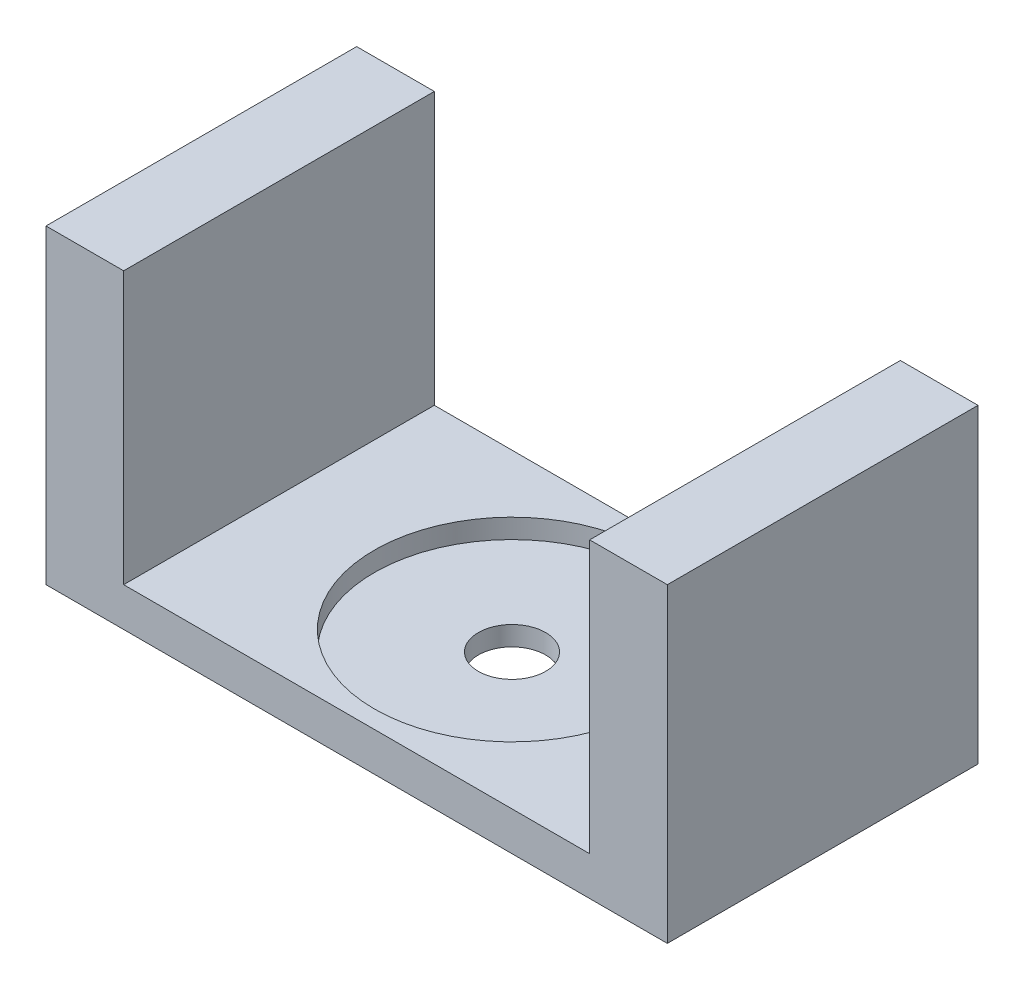
SolidWorks part; units mm, degrees
material "6063-O"
ref_plane "Front" through (0, 0, 0) normal (0, 0, 1) x (1, 0, 0)
ref_plane "Top" through (0, 0, 0) normal (0, 1, 0) x (1, 0, 0)
ref_plane "Right" through (0, 0, 0) normal (1, 0, 0) x (0, 0, -1)
sketch "Sketch1" plane through (0, 0, 0) normal (0, 0, 1) x (1, 0, 0)
  line L0 (0, -703.9235) -> (0, 0) construction
  line L13 (0, 6.35) -> (0, 34852.6286) construction
  line L14 (50.8, 0) -> (-50.8, 0)
  line L16 (38.1, 6.35) -> (-38.1, 6.35)
  line L19 (-38.1, 6.35) -> (-38.1, 50.8)
  line L20 (-38.1, 50.8) -> (-50.8, 50.8)
  line L21 (-50.8, 0) -> (-50.8, 50.8)
  line L22 (50.8, 0) -> (50.8, 50.8)
  line L23 (38.1, 50.8) -> (50.8, 50.8)
  line L24 (38.1, 6.35) -> (38.1, 50.8)
  dimension "D1" = 50.8
  dimension "D2" = 50.8
  dimension "D3" = 12.7
  dimension "D4" = 44.45
  dimension "D5" = 6.35
extrude "Boss-Extrude1" add sketch "Sketch1" along normal blind 50.8
sketch "Sketch2" plane through (0, 6.35, 0) normal (0, 1, 0) x (1, 0, 0)
  line L0 (0, 0) -> (0, -50.8) construction
  line L1 (38.1, -50.8) -> (-38.1, -50.8) construction
  circle A0 centre (0, -25.4) radius 22.5044
  dimension "D1" = 45.0088
extrude "Cut-Extrude1" cut sketch "Sketch2" against normal blind 3.175
sketch "Sketch3" plane through (0, 3.175, 0) normal (0, 1, 0) x (1, 0, 0)
  line L0 (0, 0) -> (0, -50.8) construction
  line L1 (38.1, -50.8) -> (-38.1, -50.8) construction
  circle A0 centre (0, -25.4) radius 5.5
  dimension "D1" = 11
extrude "Cut-Extrude2" cut sketch "Sketch3" against normal through all
